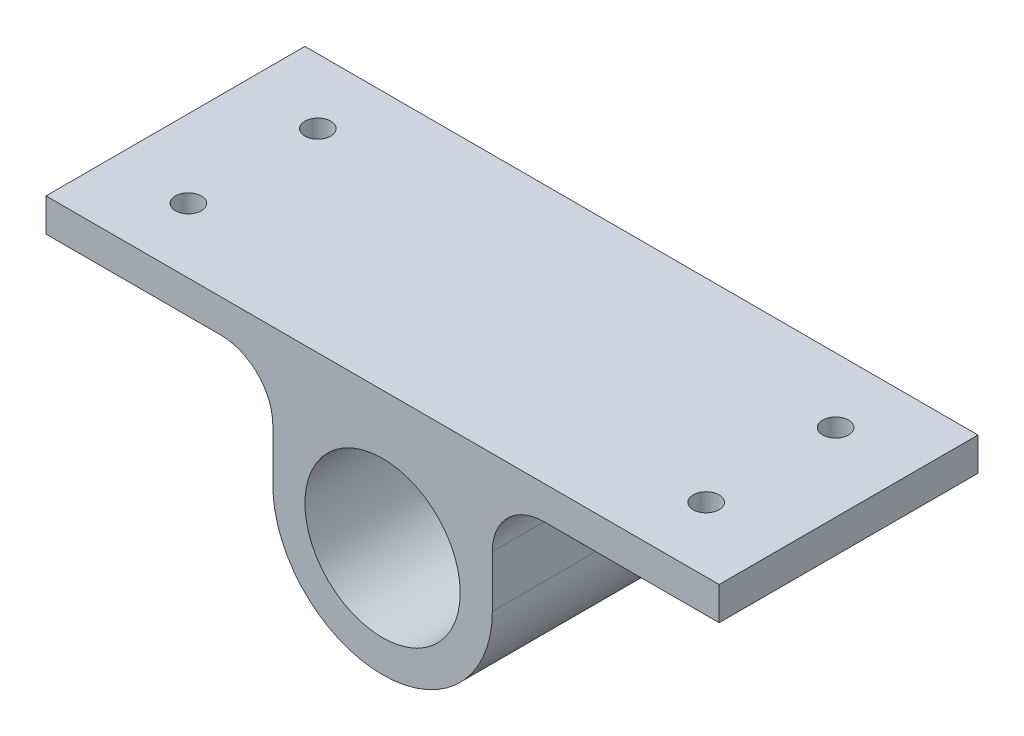
SolidWorks part; units mm, degrees
ref_plane "Front Plane" through (0, 0, 0) normal (0, 0, 1) x (1, 0, 0)
ref_plane "Top Plane" through (0, 0, 0) normal (0, 1, 0) x (1, 0, 0)
ref_plane "Right Plane" through (0, 0, 0) normal (1, 0, 0) x (0, 0, -1)
sketch "Sketch1" plane through (0, 0, 0) normal (0, 0, 1) x (1, 0, 0)
  line L0 (0, 0) -> (0, 180.2554) construction
  line L1 (-325, 132) -> (325, 132)
  line L2 (-325, 132) -> (-325, 100)
  line L3 (-325, 100) -> (-156, 100)
  line L4 (-106, 50) -> (-106, 0)
  line L5 (325, 132) -> (325, 100)
  line L6 (325, 100) -> (156, 100)
  line L7 (106, 50) -> (106, 0)
  arc A0 (-106, 0) -> (106, 0) centre (0, 0) ccw
  circle A1 centre (0, 0) radius 75
  arc A2 (156, 100) -> (106, 50) centre (156, 50) ccw
  arc A3 (-156, 100) -> (-106, 50) centre (-156, 50) cw
  dimension "D1" = 106
  dimension "D2" = 150
  dimension "D6" = 50
  dimension "D3" = 132
  dimension "D4" = 650
  dimension "D5" = 32
extrude "Boss-Extrude1" add sketch "Sketch1" along normal blind 250
sketch "Sketch2" plane through (0, 0, 0) normal (0, 1, 0) x (1, 0, 0)
  line L0 (-325, -250) -> (-325, 0) construction
  line L1 (325, 0) -> (-325, 0) construction
  circle A0 centre (-250, -62.5) radius 12.5
  circle A1 centre (250, -62.5) radius 12.5
  circle A2 centre (250, -187.5) radius 12.5
  circle A3 centre (-250, -187.5) radius 12.5
  point P12 (0, 0)
  point P13 (0, 0)
  point P14 (0, 0)
  point P15 (0, 0)
  dimension "D1" = 75
  dimension "D3" = 25
  dimension "D4" = 125
  dimension "D2" = 62.5
  dimension "D5" = 500
extrude "Cut-Extrude1" cut sketch "Sketch2" along normal through all from surface at 100 starting at face at (-240.5, 100, 125)
